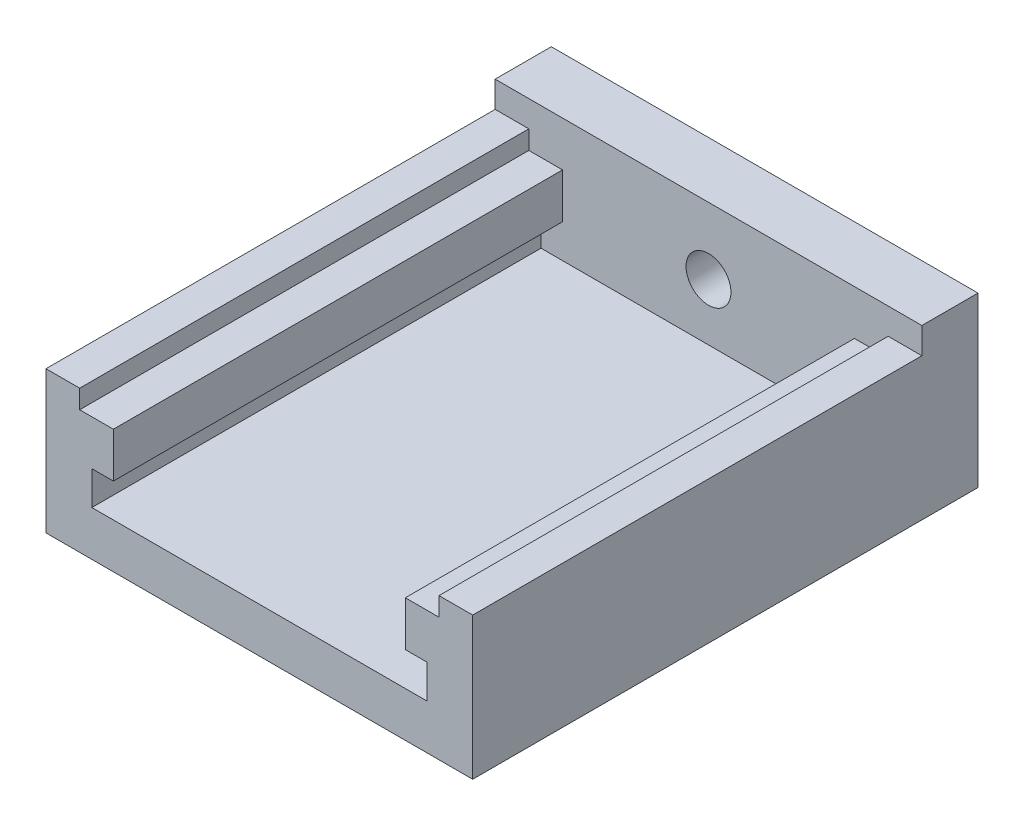
SolidWorks part; units mm, degrees
ref_plane "Ebene vorne" through (0, 0, 0) normal (0, 0, 1) x (1, 0, 0)
ref_plane "Ebene oben" through (0, 0, 0) normal (0, 1, 0) x (1, 0, 0)
ref_plane "Ebene rechts" through (0, 0, 0) normal (1, 0, 0) x (0, 0, -1)
sketch "Skizze1" plane through (0, 0, 0) normal (0, 0, 1) x (1, 0, 0)
  line L0 (-16, 1.9425) -> (-13, 1.9425)
  line L1 (-13, 1.9425) -> (-13, -2.0575)
  line L2 (-13, -2.0575) -> (-14.9167, -2.0575)
  line L3 (-14.9167, -2.0575) -> (-14.9167, -5.0575)
  line L4 (-14.9167, -5.0575) -> (14.9167, -5.0575)
  line L5 (0, -9.0575) -> (0, 9.3528) construction
  line L6 (19, -9.0575) -> (-19, -9.0575)
  line L7 (-19, -9.0575) -> (-19, 3.6092)
  line L8 (-19, 3.6092) -> (-16, 3.6092)
  line L9 (-16, 3.6092) -> (-16, 1.9425)
  line L10 (16, 3.6092) -> (16, 1.9425)
  line L11 (19, 3.6092) -> (16, 3.6092)
  line L12 (19, -9.0575) -> (19, 3.6092)
  line L13 (14.9167, -2.0575) -> (14.9167, -5.0575)
  line L14 (13, -2.0575) -> (14.9167, -2.0575)
  line L15 (13, 1.9425) -> (13, -2.0575)
  line L16 (16, 1.9425) -> (13, 1.9425)
  point P15 (0, -5.0575)
  dimension "D1" = 3
  dimension "D2" = 4
  dimension "D3" = 4
  dimension "D4" = 3
  dimension "D5" = 3
  dimension "D6" = 26
extrude "Aufsatz-Linear austragen1" add sketch "Skizze1" along normal blind 40
sketch "Skizze2" plane through (0, 0, 0) normal (0, 0, -1) x (-1, 0, 0)
  line L0 (19, 3.6092) -> (19, -9.0575) construction
  line L1 (-19, -9.0575) -> (19, -9.0575)
  line L2 (-19, -9.0575) -> (-19, 5.9425)
  line L3 (-19, 5.9425) -> (19, 5.9425)
  line L4 (19, -9.0575) -> (19, 5.9425)
  circle A0 centre (0, 0) radius 2
  point P5 (0, 0)
  dimension "D2" = 4
  dimension "D1" = 15
extrude "Aufsatz-Linear austragen2" add sketch "Skizze2" along normal blind 5
